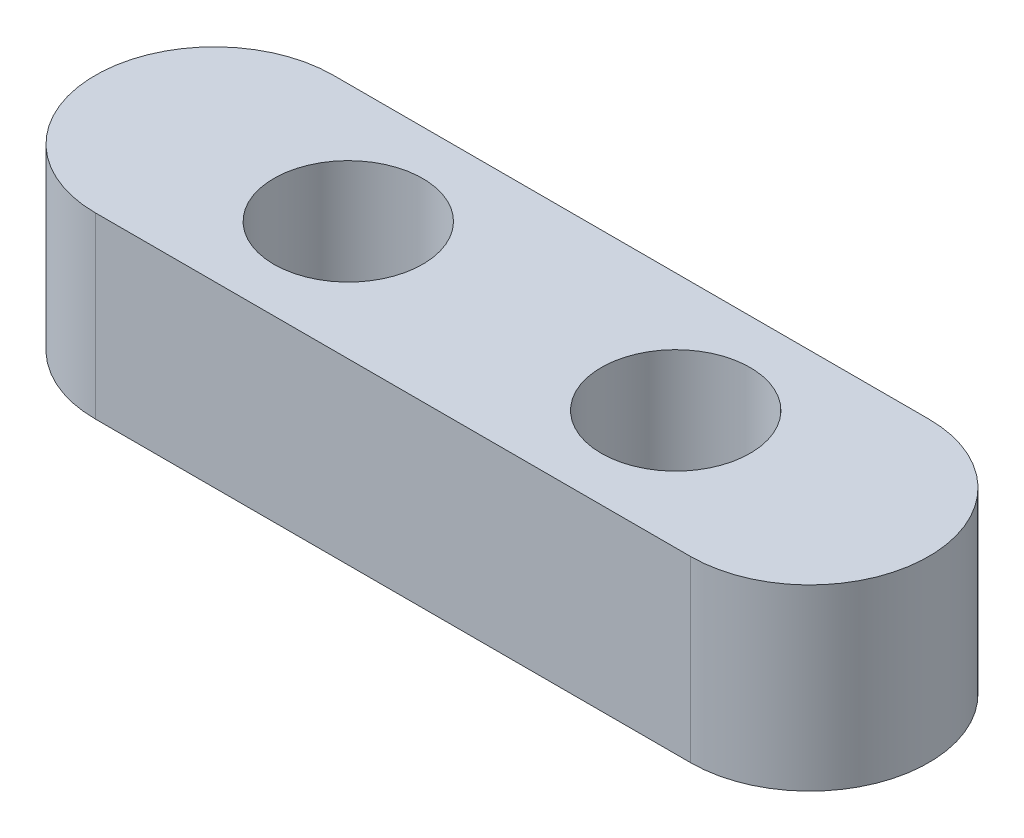
SolidWorks part; units mm, degrees
ref_plane "Front" through (0, 0, 0) normal (0, 0, 1) x (1, 0, 0)
ref_plane "Top" through (0, 0, 0) normal (0, 1, 0) x (1, 0, 0)
ref_plane "Right" through (0, 0, 0) normal (1, 0, 0) x (0, 0, -1)
sketch "Sketch2" plane through (0, 0, 0) normal (0, 1, 0) x (1, 0, 0)
  line L0 (-10, 0) -> (10, 0) construction
  line L1 (-10, 4) -> (10, 4)
  line L2 (-10, -4) -> (10, -4)
  arc A0 (-10, 4) -> (-10, -4) centre (-10, 0) ccw
  arc A1 (10, -4) -> (10, 4) centre (10, 0) ccw
  circle A2 centre (-5.5, 0) radius 2.5
  circle A3 centre (5.5, 0) radius 2.5
  point P2 (0, 0)
  point P12 (0, 0)
  point P13 (0, 0)
  point P14 (0, 0)
  point P15 (0, 0)
  dimension "D3" = 5
  dimension "D4" = 5
  dimension "D1" = 8
  dimension "D2" = 20
  dimension "D5" = 11
  dimension "D6" = 5.5
extrude "Boss-Extrude1" add sketch "Sketch2" along normal blind 6
equation "\"D4@Sketch2\"=\"D3@Sketch2\""
equation "\"D6@Sketch2\"=\"D5@Sketch2\"/2"
